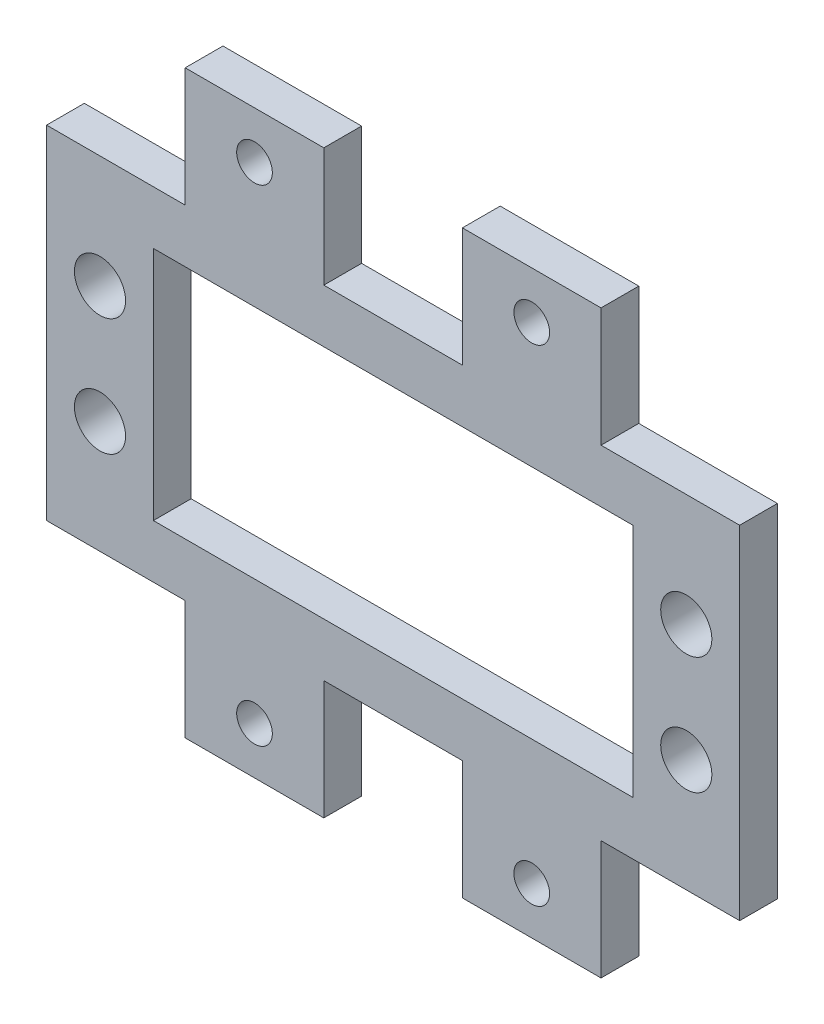
SolidWorks part; units mm, degrees
ref_plane "Front Plane" through (0, 0, 0) normal (0, 0, 1) x (1, 0, 0)
ref_plane "Top Plane" through (0, 0, 0) normal (0, 1, 0) x (1, 0, 0)
ref_plane "Right Plane" through (0, 0, 0) normal (1, 0, 0) x (0, 0, -1)
sketch "Sketch2" plane through (0, 0, 0) normal (0, 0, 1) x (1, 0, 0)
  line L0 (23.312, 14.4) -> (29.14, 14.4)
  line L2 (0, 0) -> (0, 14.4)
  line L3 (0, 14.4) -> (11.656, 14.4)
  line L5 (8.98, 9.91) -> (29.14, 9.91)
  line L6 (8.98, 9.91) -> (8.98, 0)
  line L12 (29.14, 9.91) -> (29.14, 14.4)
  line L13 (8.98, 0) -> (0, 0)
  line L24 (11.656, 14.4) -> (11.656, 24.4)
  line L25 (11.656, 24.4) -> (23.312, 24.4)
  line L26 (23.312, 14.4) -> (23.312, 24.4)
  circle A0 centre (4.49, 4.935) radius 2.15
  circle A1 centre (17.484, 20.4312) radius 1.5
  dimension "D4" = 4.3
  dimension "D13" = 5.828
  dimension "D7" = 5.828
  dimension "D3" = 8.98
  dimension "D10" = 3
  dimension "D2" = 9.91
  dimension "D5" = 4.49
  dimension "D6" = 20.16
  dimension "D8" = 4.935
  dimension "D9" = 3.9688
  dimension "D11" = 11.656
  dimension "D12" = 10
  dimension "D15" = 4.49
  dimension "D16" = 4.49
extrude "Boss-Extrude1" add sketch "Sketch2" along normal blind 3.175
mirror "Mirror8" about plane through (8.98, 0, 3.175) normal (0, 1, 0) of "Boss-Extrude1"
mirror "Mirror10" about plane through (29.14, 9.91, 3.175) normal (-1, 0, 0) of bodies 103
